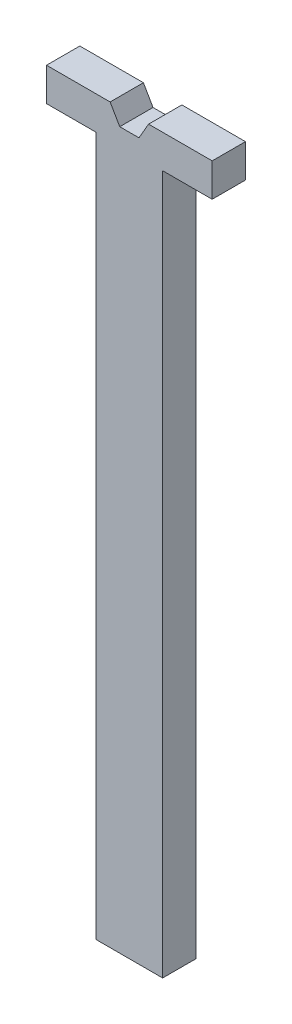
SolidWorks part; units mm, degrees
ref_plane "Front Plane" through (0, 0, 0) normal (0, 0, 1) x (1, 0, 0)
ref_plane "Top Plane" through (0, 0, 0) normal (0, 1, 0) x (1, 0, 0)
ref_plane "Right Plane" through (0, 0, 0) normal (1, 0, 0) x (0, 0, -1)
sketch "Sketch1" plane through (0, 0, 0) normal (0, 0, 1) x (1, 0, 0)
  line L0 (-10, -15) -> (10, -15)
  line L1 (-24.875, -5) -> (24.875, -5)
  line L2 (-24.875, -5) -> (-24.875, 5)
  line L3 (-24.875, 5) -> (24.875, 5)
  line L4 (24.875, -5) -> (24.875, 5)
  line L5 (-24.875, -5) -> (24.875, 5) construction
  line L6 (-24.875, 5) -> (24.875, -5) construction
  line L7 (-10, -15) -> (10, -15)
  line L8 (-10, -15) -> (-10, 5)
  line L9 (-10, 5) -> (10, 5)
  line L10 (10, -15) -> (10, 5)
  line L11 (-10, -15) -> (10, 5) construction
  line L12 (-10, 5) -> (10, -15) construction
  line L13 (5.7735, 5) -> (2.8868, 10)
  line L14 (2.8868, 10) -> (-2.8868, 10)
  line L15 (-2.8868, 10) -> (-5.7735, 5)
  line L16 (-5.7735, 5) -> (-2.8868, 0)
  line L17 (-2.8868, 0) -> (2.8868, 0)
  line L18 (2.8868, 0) -> (5.7735, 5)
  line L19 (-10, -15) -> (-10, -215)
  line L20 (10, -15) -> (10, -215)
  line L21 (-10, -215) -> (10, -215)
  circle A0 centre (0, 5) radius 5 construction
  point P0 (0, 0)
  point P6 (0, -5)
  dimension "D1" = 49.75
  dimension "D2" = 20
  dimension "D3" = 10
extrude "Boss-Extrude1" add sketch "Sketch1" along normal blind 10 contours L19 L21 L20 L0 | L0 L10 L1 L8 | L18 L17 L16 L3 L8 L1 L10 L9 | L1 L8 L3 L2 | L10 L1 L4 L3
